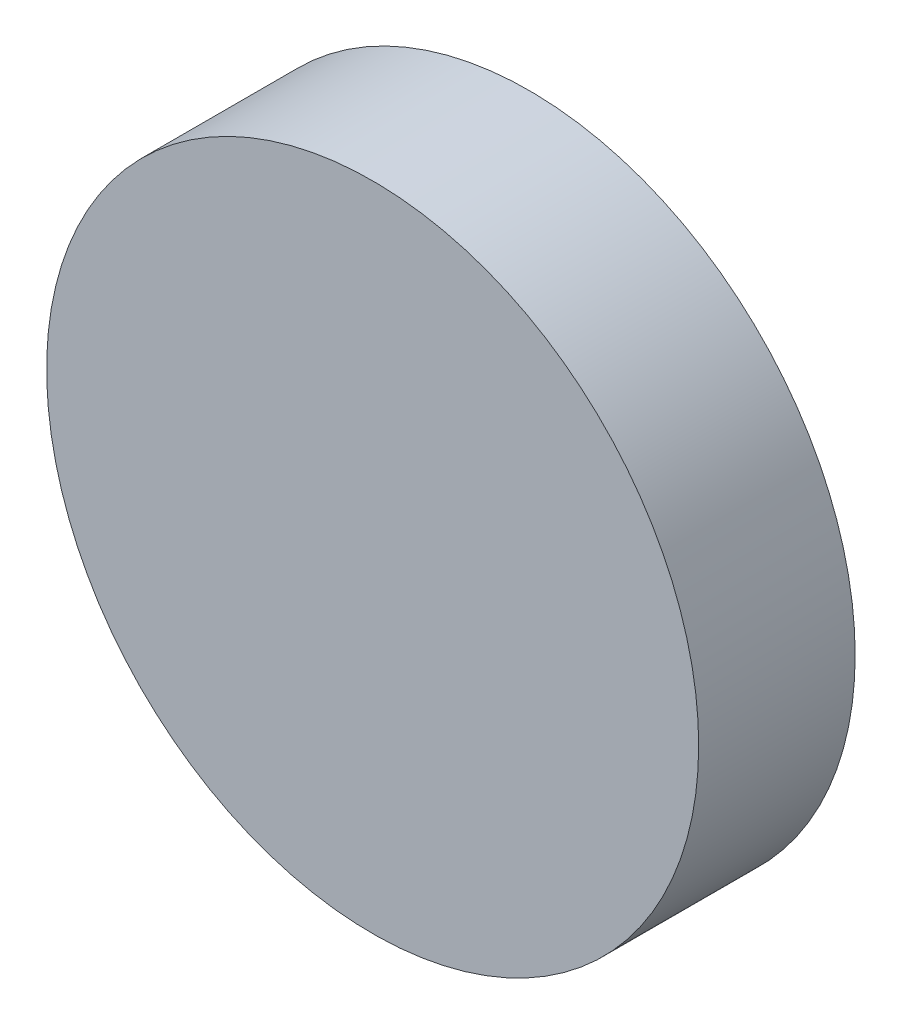
SolidWorks part; units mm, degrees
ref_plane "前视基准面" through (0, 0, 0) normal (0, 0, 1) x (1, 0, 0)
ref_plane "上视基准面" through (0, 0, 0) normal (0, 1, 0) x (1, 0, 0)
ref_plane "右视基准面" through (0, 0, 0) normal (1, 0, 0) x (0, 0, -1)
sketch "草图1" plane through (0, 0, 0) normal (0, 0, 1) x (1, 0, 0)
  circle A0 centre (0, 0) radius 12.5
  dimension "D1" = 25
extrude "凸台-拉伸1" add sketch "草图1" along normal blind 6
